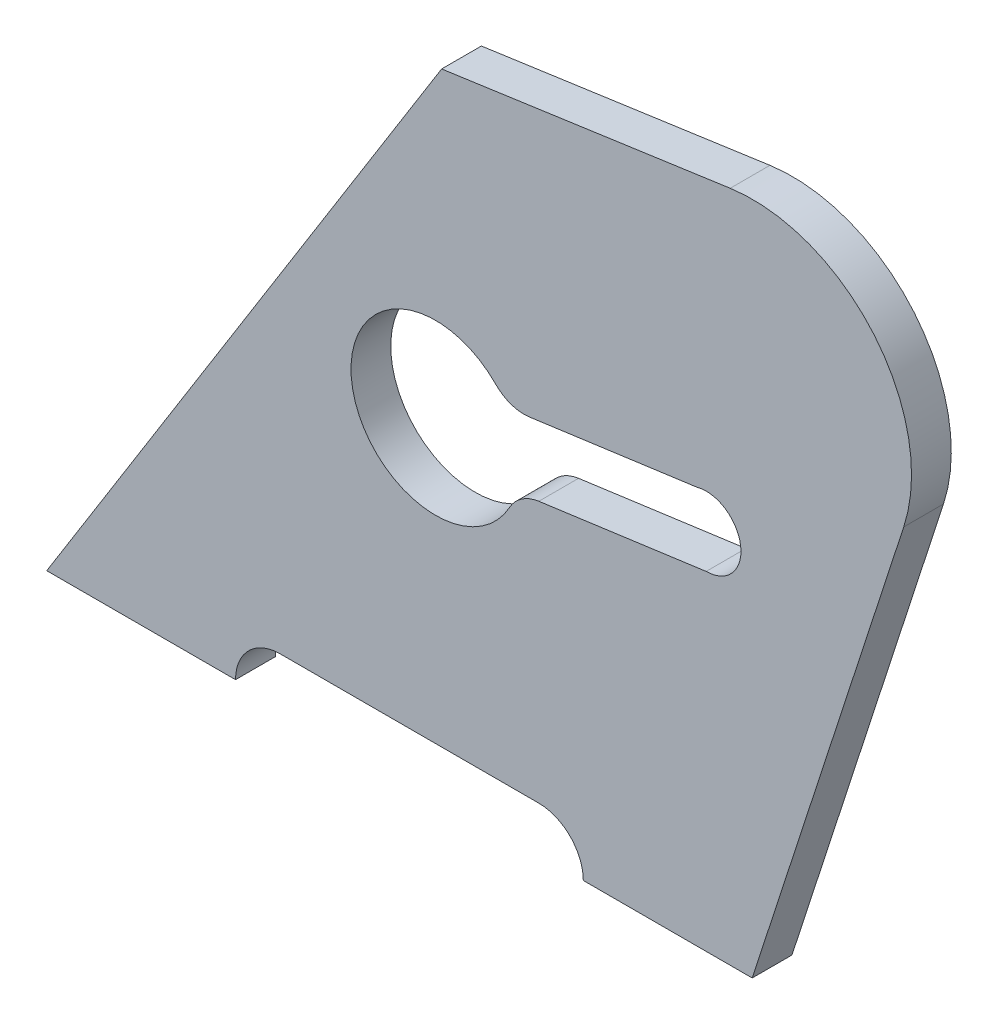
SolidWorks part; units mm, degrees
ref_plane "Front Plane" through (0, 0, 0) normal (0, 0, 1) x (1, 0, 0)
ref_plane "Top Plane" through (0, 0, 0) normal (0, 1, 0) x (1, 0, 0)
ref_plane "Right Plane" through (0, 0, 0) normal (1, 0, 0) x (0, 0, -1)
sketch "Sketch1" plane through (0, 0, 0) normal (0, 0, 1) x (1, 0, 0)
  line L0 (0, 0) -> (38, 0)
  line L1 (142, 0) -> (172.5035, 93.8803)
  line L2 (137.573, 135.4513) -> (79.4879, 127.2072)
  line L3 (79.4879, 127.2072) -> (0, 0)
  line L4 (37.6243, 60.2114) -> (61.4021, 63.4698) construction
  line L5 (132.7354, 80.2448) -> (97.1659, 75.3706)
  line L6 (134.6185, 66.5028) -> (99.049, 61.6286)
  line L7 (47, 9) -> (99, 9)
  line L8 (139.6706, 74.1951) -> (167.3394, 77.9866) construction
  line L9 (108, 0) -> (142, 0)
  arc A0 (90.3726, 77.6905) -> (93.1302, 57.5667) centre (78.2447, 65.7777) ccw
  arc A1 (132.7354, 66.2448) -> (130.8523, 79.9867) centre (132.7354, 73.2448) ccw
  arc A3 (108, 0) -> (99, 9) centre (99, 0) ccw
  arc A4 (47, 9) -> (38, 0) centre (47, 0) ccw
  arc A5 (172.5035, 93.8803) -> (137.573, 135.4513) centre (142.0697, 103.7688) ccw
  arc A6 (99.049, 61.6286) -> (93.1302, 57.5667) centre (100.1351, 53.7027) ccw
  arc A7 (97.1659, 75.3706) -> (90.3726, 77.6905) centre (96.0798, 83.2965) cw
  point P25 (188.3525, 142.6585)
  dimension "D6" = 14
  dimension "D7" = 34
  dimension "D14" = 32
  dimension "D15" = 8
  dimension "D16" = 9
  dimension "D1" = 58
  dimension "D2" = 108
  dimension "D3" = 150
  dimension "D4" = 142
  dimension "D5" = 150
  dimension "D8" = 55
  dimension "D9" = 41
  dimension "D10" = 71
  dimension "D11" = 82
  dimension "D12" = 52
  dimension "D13" = 47
extrude "Boss-Extrude1" add sketch "Sketch1" along normal blind 8 contours L1 A5 L2 L3 L0 A4 L7 A3 L9 A7 L5 A1 L6 A6 A0
